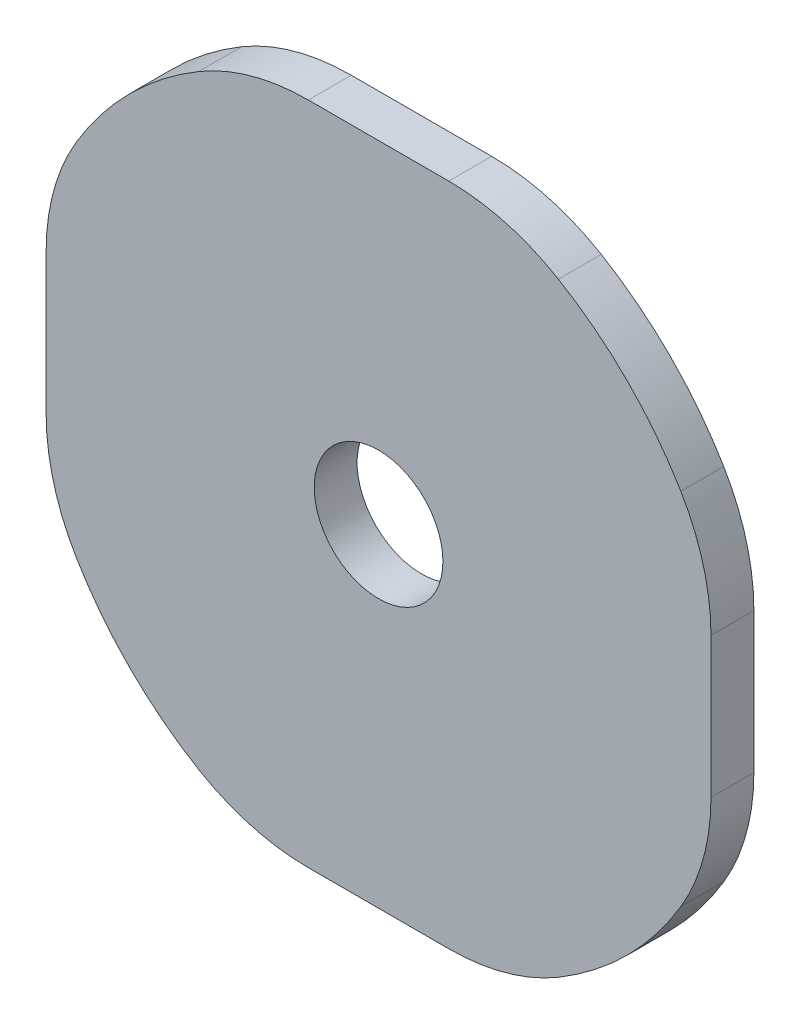
SolidWorks part; units mm, degrees
ref_plane "Plan de face" through (0, 0, 0) normal (0, 0, 1) x (1, 0, 0)
ref_plane "Plan de dessus" through (0, 0, 0) normal (0, 1, 0) x (1, 0, 0)
ref_plane "Plan de droite" through (0, 0, 0) normal (1, 0, 0) x (0, 0, -1)
sketch "Esquisse1" plane through (0, 0, 0) normal (0, 0, 1) x (1, 0, 0)
  circle A0 centre (0, 0) radius 16.4
  dimension "D1" = 32.8
extrude "Boss.-Extru.1" add sketch "Esquisse1" along normal blind 2
sketch "Esquisse3" plane through (0, 0, 2) normal (0, 0, 1) x (1, 0, 0)
  circle A0 centre (0, 0) radius 3
  dimension "D1" = 6
extrude "Enlèv. mat.-Extru.1" cut sketch "Esquisse3" against normal through all
sketch "Esquisse4" plane through (0, 0, 0) normal (0, 0, -1) x (-1, 0, 0)
  line L0 (-15.5, 0) -> (15.5, 0) construction
  line L1 (-15.5, 15.5) -> (15.5, 15.5)
  line L2 (-15.5, 15.5) -> (-15.5, -15.5)
  line L3 (-15.5, -15.5) -> (15.5, -15.5)
  line L4 (15.5, 15.5) -> (15.5, -15.5)
  line L6 (-36.1182, 22.3769) -> (35.9922, 22.3769)
  line L7 (-36.1182, 22.3769) -> (-36.1182, -24.331)
  line L8 (-36.1182, -24.331) -> (35.9922, -24.331)
  line L9 (35.9922, 22.3769) -> (35.9922, -24.331)
  dimension "D1" = 31
  dimension "D2" = 31
extrude "Enlèv. mat.-Extru.2" cut sketch "Esquisse4" against normal blind 10
fillet "Congé1" radius 10 8 edges at (5.3582, 15.5, 1) (-5.3582, 15.5, 1) (-15.5, 5.3582, 1) (-15.5, -5.3582, 1) (-5.3582, -15.5, 1) (5.3582, -15.5, 1) (15.5, -5.3582, 1) (15.5, 5.3582, 1)
